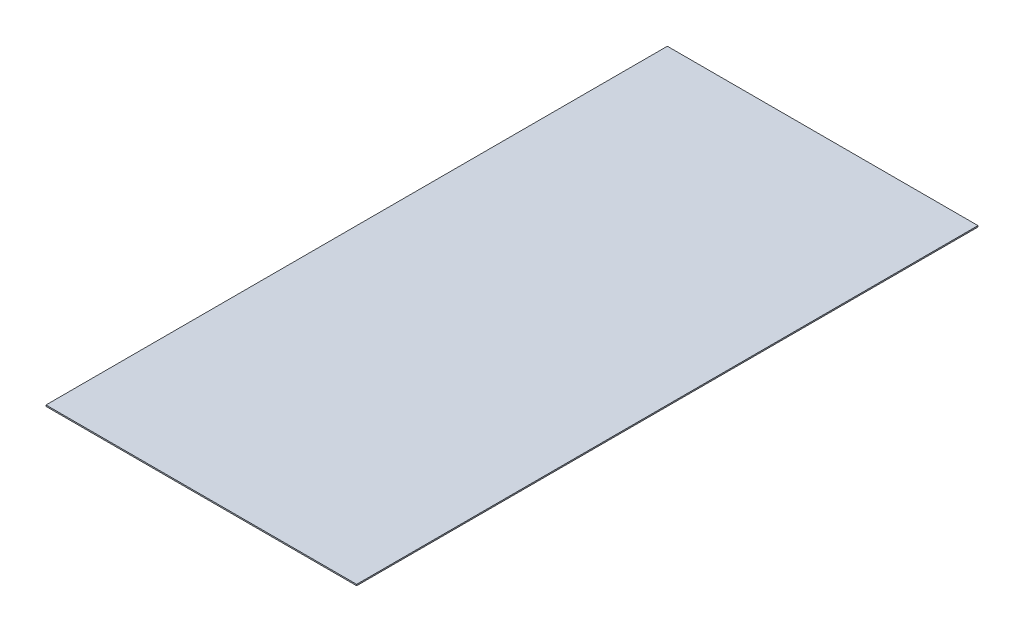
SolidWorks part; units mm, degrees
material "柚木"
ref_plane "前视基准面" through (0, 0, 0) normal (0, 0, 1) x (1, 0, 0)
ref_plane "上视基准面" through (0, 0, 0) normal (0, 1, 0) x (1, 0, 0)
ref_plane "右视基准面" through (0, 0, 0) normal (1, 0, 0) x (0, 0, -1)
sketch "草图1" plane through (0, 0, 0) normal (0, 1, 0) x (1, 0, 0)
  line L1 (-610, -1220) -> (610, -1220)
  line L2 (-610, -1220) -> (-610, 1220)
  line L3 (-610, 1220) -> (610, 1220)
  line L4 (610, -1220) -> (610, 1220)
  line L5 (-610, -1220) -> (610, 1220) construction
  line L6 (-610, 1220) -> (610, -1220) construction
  point P0 (0, 0)
  dimension "D1" = 1220
  dimension "D2" = 2440
extrude "凸台-拉伸1" add sketch "草图1" along normal blind 5
